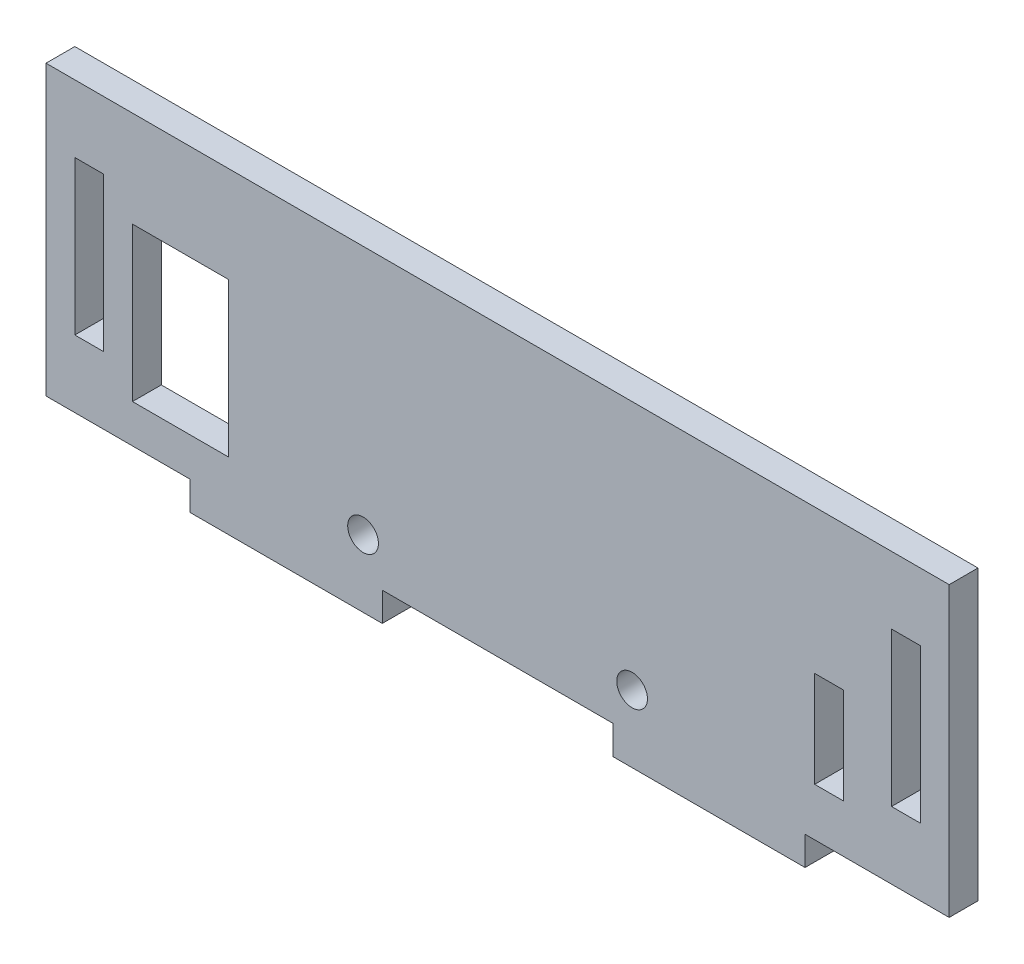
SolidWorks part; units mm, degrees
ref_plane "前视基准面" through (0, 0, 0) normal (0, 0, 1) x (1, 0, 0)
ref_plane "上视基准面" through (0, 0, 0) normal (0, 1, 0) x (1, 0, 0)
ref_plane "右视基准面" through (0, 0, 0) normal (1, 0, 0) x (0, 0, -1)
sketch "草图1" plane through (0, 0, 0) normal (0, 0, 1) x (1, 0, 0)
  line L0 (44, 0) -> (44, 4)
  line L1 (0, 0) -> (12, 0)
  line L2 (0, 7) -> (0, 30)
  line L3 (0, 30) -> (88, 30)
  line L4 (88, 7) -> (88, 30)
  line L5 (44, 4) -> (53.45, 4)
  line L6 (55, 4) -> (44, 4)
  line L7 (44, 4) -> (33, 4)
  line L8 (0, 0) -> (12, 0)
  line L9 (12, 0) -> (12, -3)
  line L10 (12, -3) -> (32, -3)
  line L11 (32, -3) -> (32, 0)
  line L12 (88, 0) -> (76, 0)
  line L13 (76, 0) -> (76, -3)
  line L14 (76, -3) -> (56, -3)
  line L15 (56, -3) -> (56, 0)
  line L16 (76, 0) -> (88, 0)
  line L18 (88, 15) -> (88, 23)
  line L19 (88, 23) -> (85, 23)
  line L20 (85, 15) -> (85, 23)
  line L22 (88, 15) -> (88, 7)
  line L23 (88, 7) -> (85, 7)
  line L24 (85, 15) -> (85, 7)
  line L25 (88, 30) -> (91, 30)
  line L26 (88, 30) -> (88, 7)
  line L27 (88, 0) -> (91, 0)
  line L28 (91, 30) -> (91, 0)
  line L30 (0, 15) -> (0, 23)
  line L31 (0, 23) -> (3, 23)
  line L32 (3, 15) -> (3, 23)
  line L34 (0, 15) -> (0, 7)
  line L35 (0, 7) -> (3, 7)
  line L36 (3, 15) -> (3, 7)
  line L37 (0, 30) -> (-3, 30)
  line L38 (0, 30) -> (0, 7)
  line L39 (0, 0) -> (-3, 0)
  line L40 (-3, 30) -> (-3, 0)
  line L41 (32, 0) -> (56, 0)
  line L42 (3, 7) -> (6, 7)
  line L43 (6, 7) -> (6, 20)
  line L44 (6, 20) -> (6, 7)
  line L45 (6, 7) -> (6, 4)
  line L46 (6, 4) -> (11, 4)
  line L47 (85, 15) -> (80, 15)
  line L48 (11, 20) -> (6, 20)
  line L49 (44, 4) -> (30, 4)
  line L50 (44, 4) -> (58, 4)
  line L52 (11, 20) -> (16, 20)
  line L54 (11, 4) -> (16, 4)
  line L55 (16, 20) -> (16, 4)
  line L56 (80, 15) -> (77, 15)
  line L57 (80, 15) -> (80, 5)
  line L58 (80, 5) -> (77, 5)
  line L59 (77, 15) -> (77, 5)
  circle A2 centre (30, 4) radius 1.6
  circle A3 centre (58, 4) radius 1.6
extrude "凸台-拉伸1" add sketch "草图1" along normal blind 3
